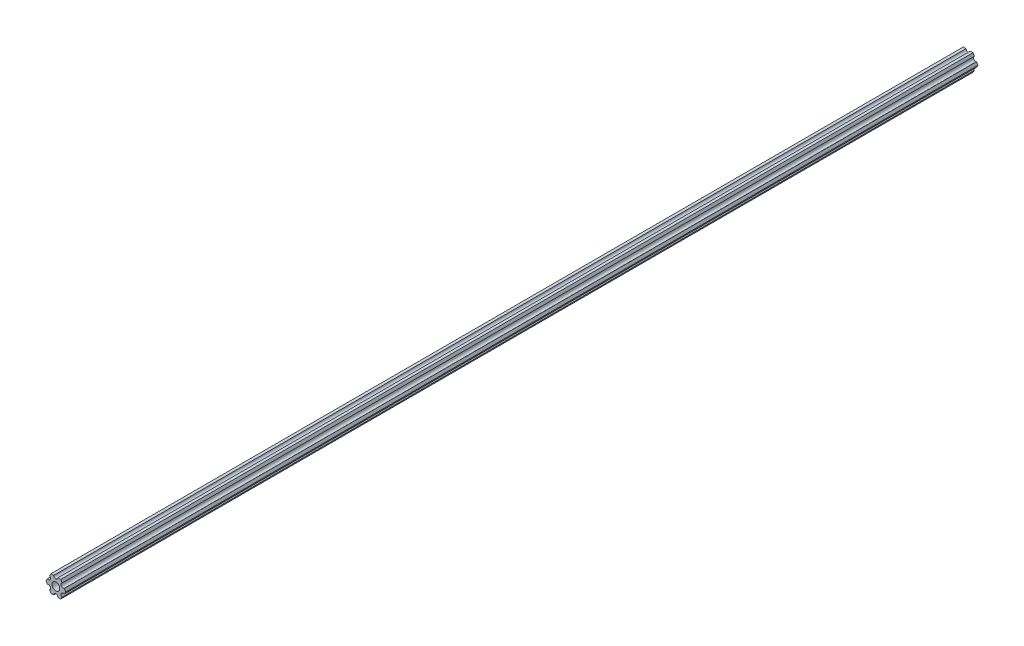
SolidWorks part; units mm, degrees
material "6061-T6 (SS)"
ref_plane "Front Plane" through (0, 0, 0) normal (0, 0, 1) x (1, 0, 0)
ref_plane "Top Plane" through (0, 0, 0) normal (0, 1, 0) x (1, 0, 0)
ref_plane "Right Plane" through (0, 0, 0) normal (1, 0, 0) x (0, 0, -1)
sketch "Sketch1" plane through (0, 0, 0) normal (0, 0, 1) x (1, 0, 0)
  line L0 (-4.7055, -4.5498) -> (-3.6662, -6.35)
  line L1 (-3.6662, -6.35) -> (-1.5875, -6.35)
  line L2 (1.5875, -6.35) -> (3.6662, -6.35)
  line L3 (3.6662, -6.35) -> (4.7055, -4.5498)
  line L4 (6.293, -1.8002) -> (7.3323, 0)
  line L5 (7.3323, 0) -> (6.293, 1.8002)
  line L6 (4.7055, 4.5498) -> (3.6662, 6.35)
  line L7 (3.6662, 6.35) -> (1.5875, 6.35)
  line L8 (-1.5875, 6.35) -> (-3.6662, 6.35)
  line L9 (-3.6662, 6.35) -> (-4.7055, 4.5498)
  line L10 (-6.293, 1.8002) -> (-7.3323, 0)
  line L11 (-7.3323, 0) -> (-6.293, -1.8002)
  circle A0 centre (0, 0) radius 2.9337
  arc A1 (-6.293, -1.8002) -> (-4.7055, -4.5498) centre (-5.4993, -3.175) cw
  arc A2 (-1.5875, -6.35) -> (1.5875, -6.35) centre (0, -6.35) cw
  arc A3 (4.7055, -4.5498) -> (6.293, -1.8002) centre (5.4993, -3.175) cw
  arc A4 (6.293, 1.8002) -> (4.7055, 4.5498) centre (5.4993, 3.175) cw
  arc A5 (1.5875, 6.35) -> (-1.5875, 6.35) centre (0, 6.35) cw
  arc A6 (-4.7055, 4.5498) -> (-6.293, 1.8002) centre (-5.4993, 3.175) cw
extrude "Boss-Extrude1" add sketch "Sketch1" against normal blind 681.0248
